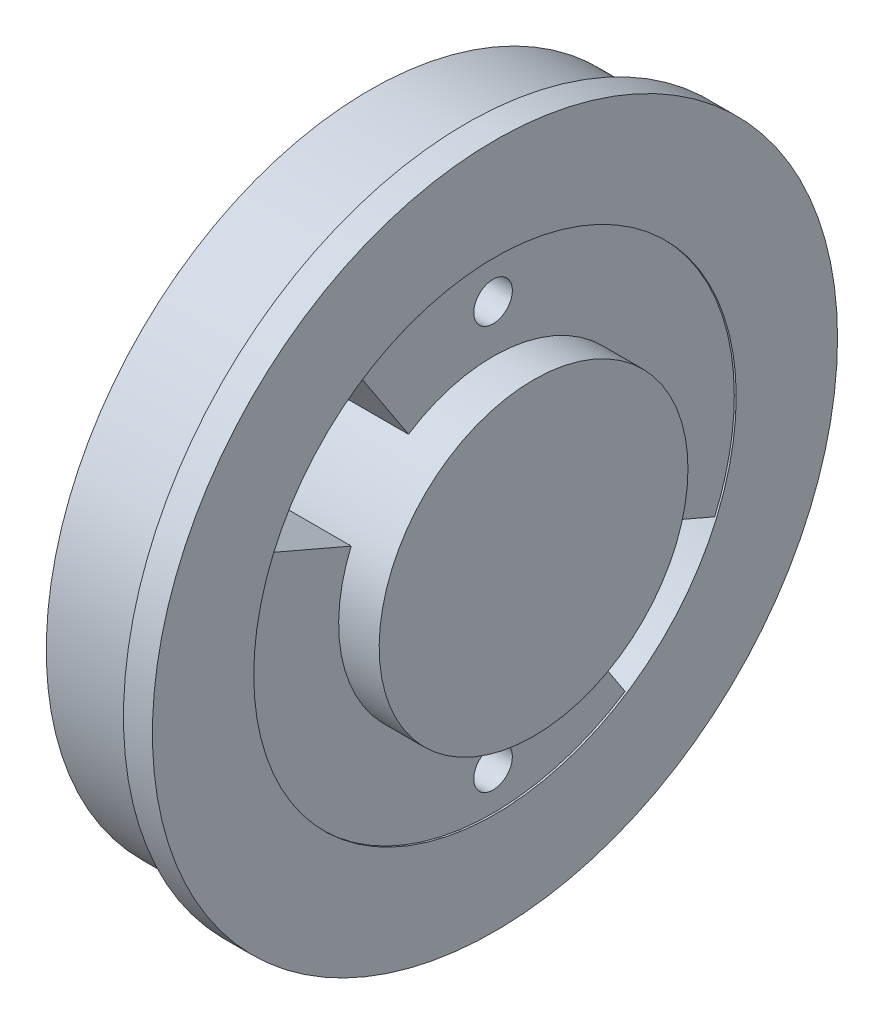
SolidWorks part; units mm, degrees
ref_plane "Front Plane" through (0, 0, 0) normal (0, 0, 1) x (1, 0, 0)
ref_plane "Top Plane" through (0, 0, 0) normal (0, 1, 0) x (1, 0, 0)
ref_plane "Right Plane" through (0, 0, 0) normal (1, 0, 0) x (0, 0, -1)
sketch "Sketch1" plane through (0, 0, 0) normal (1, 0, 0) x (0, 0, -1)
  circle A0 centre (0, 0) radius 16.75
  dimension "D1" = 33.5
extrude "Extrude1" add sketch "Sketch1" along normal blind 5
sketch "Sketch2" plane through (5, 0, 0) normal (1, 0, 0) x (0, 0, -1)
  circle A0 centre (0, 0) radius 17.75
  dimension "D1" = 35.5
extrude "Extrude2" add sketch "Sketch2" along normal blind 1.5
sketch "Sketch3" plane through (6.5, 0, 0) normal (1, 0, 0) x (0, 0, -1)
  circle A0 centre (0, 0) radius 8
  dimension "D1" = 16
extrude "Extrude3" add sketch "Sketch3" along normal blind 2
sketch "Sketch4" plane through (6.5, 0, 0) normal (1, 0, 0) x (0, 0, -1)
  circle A0 centre (0, 0) radius 12.5
  circle A1 centre (0, 0) radius 8 construction
  circle A2 centre (0, 0) radius 8
  dimension "D1" = 25
extrude "Cut-Extrude1" cut sketch "Sketch4" against normal blind 0.1
sketch "Sketch5" plane through (8.5, 0, 0) normal (1, 0, 0) x (0, 0, -1)
  line L0 (-11.4823, 4.9403) -> (-7.3487, 3.1618)
  line L1 (6.8446, -10.4595) -> (4.3805, -6.6941)
  line L2 (-4.3805, 6.6941) -> (-6.8446, 10.4595)
  line L3 (7.3487, -3.1618) -> (11.4823, -4.9403)
  arc A0 (-4.3805, 6.6941) -> (-7.3487, 3.1618) centre (0, 0) ccw
  arc A1 (-6.8446, 10.4595) -> (-11.4823, 4.9403) centre (0, 0) ccw
  arc A2 (4.3805, -6.6941) -> (7.3487, -3.1618) centre (0, 0) ccw
  arc A3 (6.8446, -10.4595) -> (11.4823, -4.9403) centre (0, 0) ccw
  circle A4 centre (0, 10.4595) radius 1
  circle A5 centre (0, -10.4595) radius 1
  dimension "D1" = 25
  dimension "D2" = 2
  dimension "D3" = 2
extrude "Cut-Extrude2" cut sketch "Sketch5" against normal blind 30.1
sketch "Sketch6" plane through (0, 0, 0) normal (-1, 0, 0) x (0, 0, 1)
  circle A3 centre (0, 0) radius 14.75
  circle A4 centre (0, 0) radius 14.75
  dimension "D1" = 2
extrude "Cut-Extrude3" cut sketch "Sketch6" against normal blind 3
